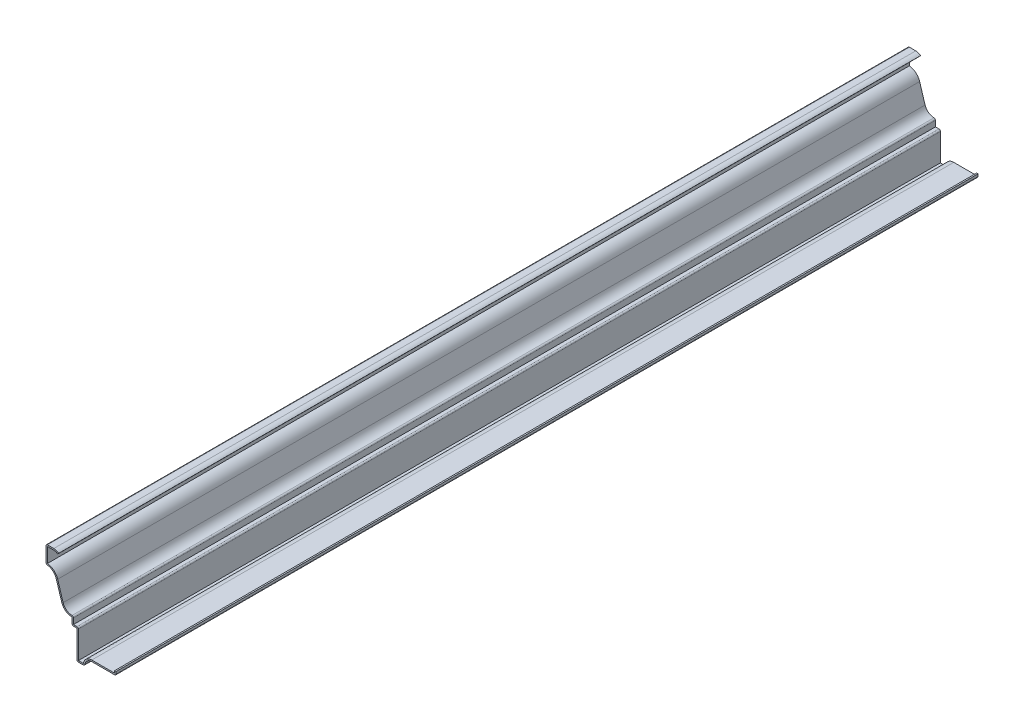
SolidWorks part; units mm, degrees
ref_plane "Front Plane" through (0, 0, 0) normal (0, 0, 1) x (1, 0, 0)
ref_plane "Top Plane" through (0, 0, 0) normal (0, 1, 0) x (1, 0, 0)
ref_plane "Right Plane" through (0, 0, 0) normal (1, 0, 0) x (0, 0, -1)
sketch "Sketch1" plane through (0, 0, 0) normal (0, 0, 1) x (1, 0, 0)
  line L0 (0, 0) -> (0, -3.175)
  line L1 (0, -3.175) -> (-21.4313, -3.175)
  line L2 (-27.7812, -9.525) -> (-34.5281, -9.525)
  line L3 (-34.5281, -9.525) -> (-34.5281, 15.875)
  line L4 (-34.5281, 15.875) -> (-38.8937, 15.875)
  line L5 (-38.8937, 15.875) -> (-38.8937, 22.225)
  line L6 (-47.9919, 28.9304) -> (-52.8144, 44.4915)
  line L7 (-61.9125, 51.1969) -> (-61.9125, 66.675)
  line L8 (-61.9125, 66.675) -> (-55.0001, 66.675)
  line L9 (-61.9125, 51.1969) -> (-38.8937, 51.1969) construction
  line L10 (-38.8937, 22.225) -> (-61.9742, 22.225) construction
  arc A0 (-21.4313, -3.175) -> (-27.7812, -9.525) centre (-21.4313, -9.525) ccw
  arc A1 (-38.8937, 22.225) -> (-47.9919, 28.9304) centre (-38.8937, 31.75) cw
  arc A2 (-61.9125, 51.1969) -> (-52.8144, 44.4915) centre (-61.9125, 41.6719) cw
  arc A3 (-55.0001, 66.675) -> (-50.8, 65.0875) centre (-55.0001, 60.325) cw
  point P12 (-54.2633, 66.675)
  point P26 (-50.4031, 36.7109)
  dimension "D13" = 9.525
  dimension "D14" = 6.35
  dimension "D1" = 3.175
  dimension "D2" = 6.35
  dimension "D3" = 27.7812
  dimension "D4" = 6.7469
  dimension "D5" = 25.4
  dimension "D6" = 4.3656
  dimension "D7" = 6.35
  dimension "D8" = 28.9719
  dimension "D9" = 23.0188
  dimension "D10" = 15.4781
  dimension "D11" = 11.1125
  dimension "D12" = 11.5094
  dimension "D15" = 1.5875
extrude "Extrude-Thin1" add sketch "Sketch1" against normal blind 762 thin
fillet "Fillet1" radius 1.27 8 edges at (-61.9125, 66.675, -381) (-61.9125, 51.1969, -381) (-38.8937, 15.875, -381) (-37.6237, 23.5933, -381) (-33.2581, 17.145, -381) (-34.5281, -9.525, -381) (-27.7813, -9.525, -381) (0, -3.175, -381)
